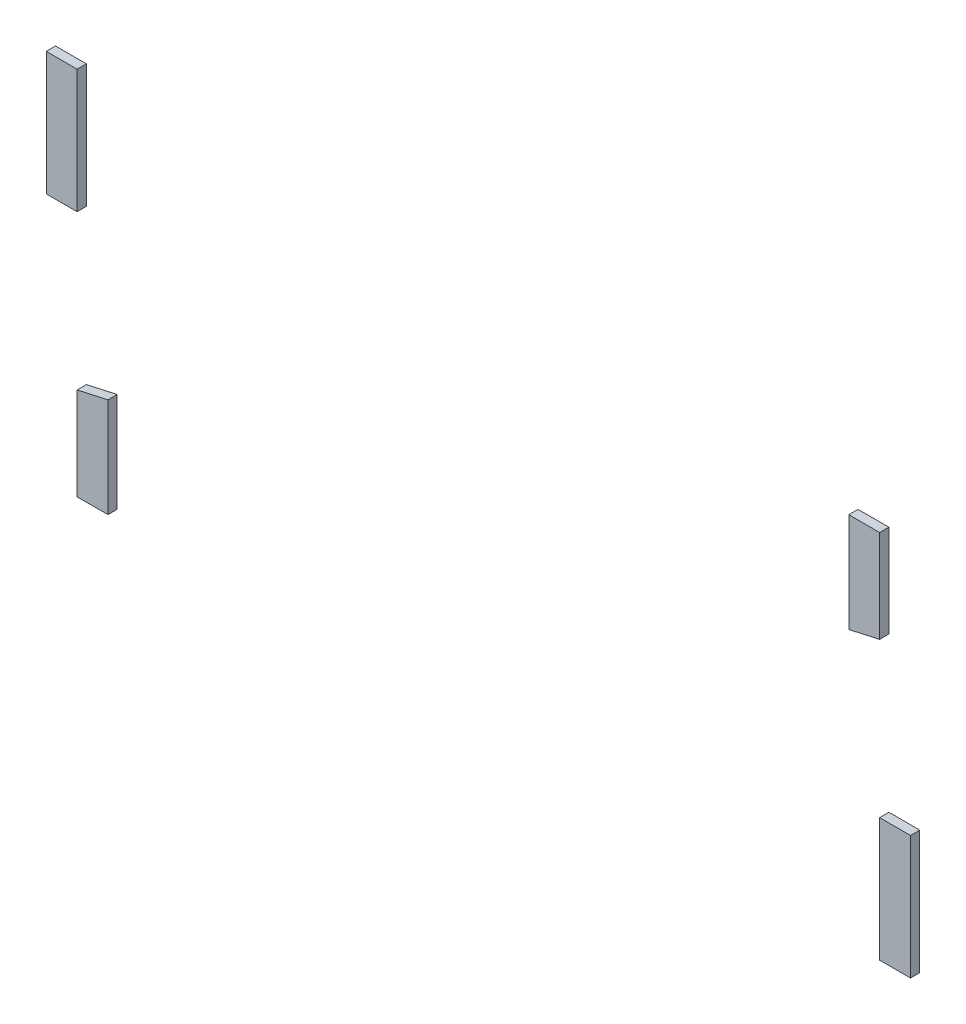
SolidWorks part; units mm, degrees
ref_plane "Front Plane" through (0, 0, 0) normal (0, 0, 1) x (1, 0, 0)
ref_plane "Top Plane" through (0, 0, 0) normal (0, 1, 0) x (1, 0, 0)
ref_plane "Right Plane" through (0, 0, 0) normal (1, 0, 0) x (0, 0, -1)
sketch "Sketch1" plane through (0, 0, 0) normal (0, 0, 1) x (1, 0, 0)
  line L1 (-35, 15) -> (-32.5, 15)
  line L2 (-35, 15) -> (-35, 5)
  line L3 (-35, 5) -> (-32.5, 5)
  line L4 (-32.5, 15) -> (-32.5, 5)
  line L6 (30, 15) -> (32.5, 15)
  line L7 (30, 15) -> (30, 6.9444)
  line L9 (32.5, 15) -> (32.5, 7.5)
  line L10 (30, 6.9444) -> (32.5, 7.5)
  line L11 (-32.5, -7.5) -> (-32.5, -15)
  line L12 (-32.5, -15) -> (-30, -15)
  line L13 (-30, -6.9444) -> (-30, -15)
  line L14 (32.5, -5) -> (35, -5)
  line L15 (32.5, -5) -> (32.5, -15)
  line L16 (32.5, -15) -> (35, -15)
  line L17 (35, -5) -> (35, -15)
  line L19 (-30, -6.9444) -> (-32.5, -7.5)
extrude "Boss-Extrude1" add sketch "Sketch1" along normal blind 0.75
